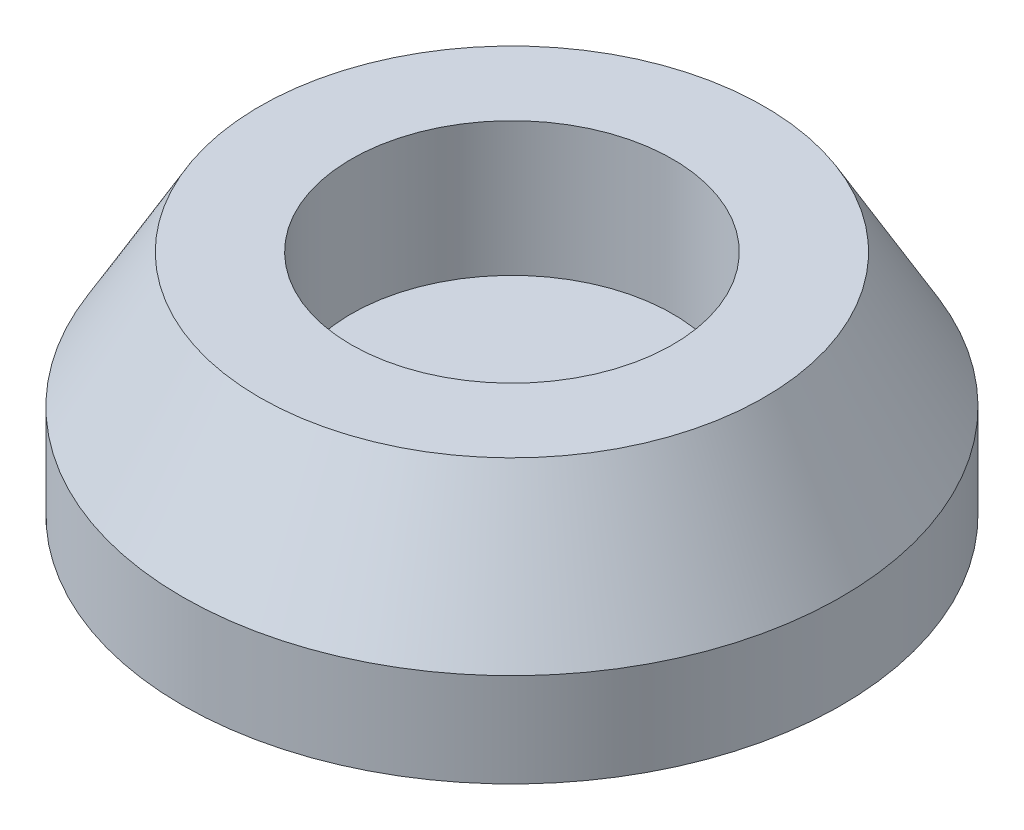
SolidWorks part; units mm, degrees
ref_plane "Front Plane" through (0, 0, 0) normal (0, 0, 1) x (1, 0, 0)
ref_plane "Top Plane" through (0, 0, 0) normal (0, 1, 0) x (1, 0, 0)
ref_plane "Right Plane" through (0, 0, 0) normal (1, 0, 0) x (0, 0, -1)
sketch "Sketch1" plane through (0, 0, 0) normal (0, 1, 0) x (1, 0, 0)
  circle A0 centre (0, 0) radius 12.3
  dimension "D1" = 24.6
extrude "Boss-Extrude1" add sketch "Sketch1" along normal blind 3.5
sketch "Sketch2" plane through (0, 3.5, 0) normal (0, 1, 0) x (1, 0, 0)
  circle A0 centre (0, 0) radius 6
  circle A1 centre (0, 0) radius 12.3
  circle A2 centre (0, 0) radius 12.3 construction
  dimension "D1" = 12
extrude "Boss-Extrude2" add sketch "Sketch2" along normal blind 5
chamfer "Chamfer1" distance 5 angle 30 1 edges at (0, 8.5, 12.3)
